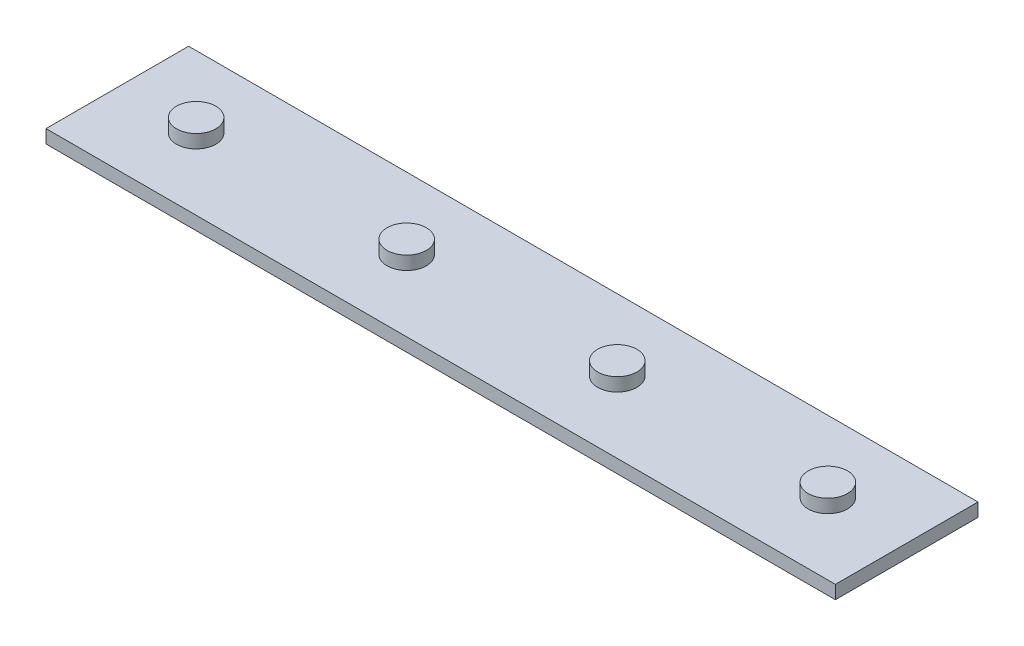
SolidWorks part; units mm, degrees
ref_plane "Front Plane" through (0, 0, 0) normal (0, 0, 1) x (1, 0, 0)
ref_plane "Top Plane" through (0, 0, 0) normal (0, 1, 0) x (1, 0, 0)
ref_plane "Right Plane" through (0, 0, 0) normal (1, 0, 0) x (0, 0, -1)
sketch "Sketch1" plane through (0, 0, 0) normal (0, 1, 0) x (1, 0, 0)
  line L1 (-140.5794, 25.4) -> (140.5794, 25.4)
  line L2 (-140.5794, 25.4) -> (-140.5794, -25.4)
  line L3 (-140.5794, -25.4) -> (140.5794, -25.4)
  line L4 (140.5794, 25.4) -> (140.5794, -25.4)
  line L5 (-140.5794, 25.4) -> (140.5794, -25.4) construction
  line L6 (-140.5794, -25.4) -> (140.5794, 25.4) construction
  point P0 (0, 0)
  dimension "D1" = 281.1589
  dimension "D2" = 50.8
extrude "Boss-Extrude1" add sketch "Sketch1" along normal blind 9.525
sketch "Sketch2" plane through (0, 9.525, 0) normal (0, 1, 0) x (1, 0, 0)
  circle A0 centre (-112.5, 0) radius 7 construction
  circle A1 centre (-37.5, 0) radius 7 construction
  circle A2 centre (37.5, 0) radius 7 construction
  circle A3 centre (112.5, 0) radius 7 construction
  circle A4 centre (-112.5, 0) radius 7
  circle A5 centre (-37.5, 0) radius 7
  circle A6 centre (37.5, 0) radius 7
  circle A7 centre (112.5, 0) radius 7
extrude "Cut-Extrude1" cut sketch "Sketch2" against normal blind 4.7625 flip side to cut
